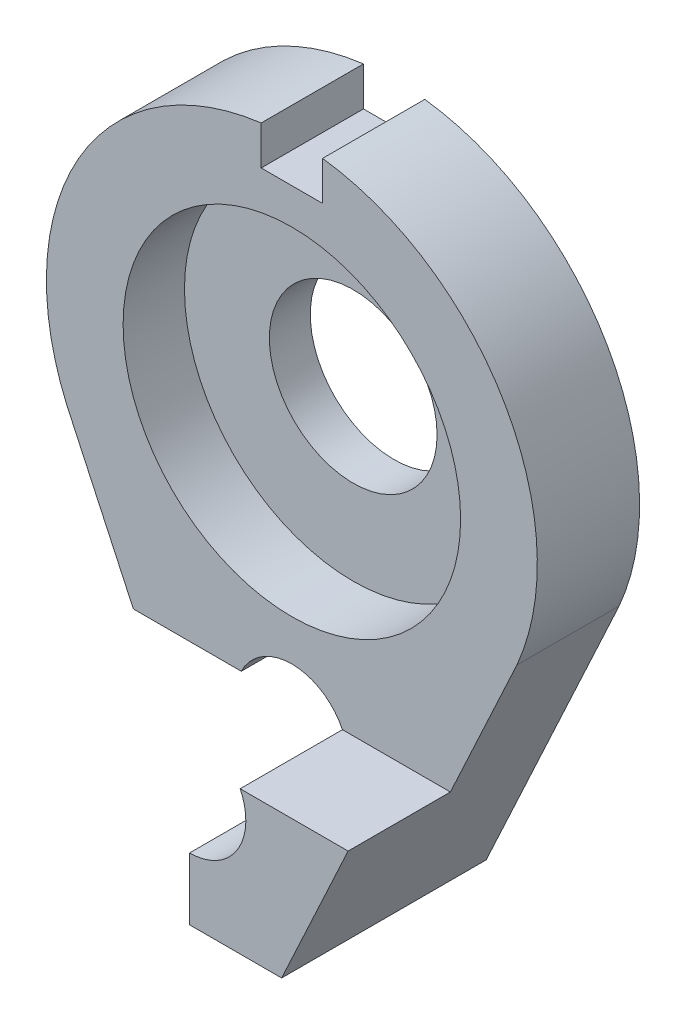
SolidWorks part; units mm, degrees
ref_plane "Plan de face" through (0, 0, 0) normal (0, 0, 1) x (1, 0, 0)
ref_plane "Plan de dessus" through (0, 0, 0) normal (0, 1, 0) x (1, 0, 0)
ref_plane "Plan de droite" through (0, 0, 0) normal (1, 0, 0) x (0, 0, -1)
sketch "Esquisse1" plane through (0, 0, 0) normal (0, 0, 1) x (1, 0, 0)
  line L0 (-11, -4.7958) -> (-4.5, -18.7958)
  line L1 (0, -55) -> (0, 55) construction
  line L2 (11, -4.7958) -> (4.5, -18.7958)
  line L3 (-4.5, -18.7958) -> (4.5, -18.7958)
  arc A0 (-11, -4.7958) -> (11, -4.7958) centre (0, 0) cw
  circle A1 centre (0, 0) radius 4.1
  dimension "D2" = 12
  dimension "D3" = 8.2
  dimension "D1" = 22
  dimension "D4" = 9
  dimension "D5" = 14
extrude "Boss.-Extru.1" add sketch "Esquisse1" along normal blind 5
sketch "Esquisse2" plane through (0, 0, 5) normal (0, 0, 1) x (1, 0, 0)
  circle A0 centre (0, 0) radius 8.25
  dimension "D1" = 16.5
extrude "Enlèv. mat.-Extru.1" cut sketch "Esquisse2" against normal blind 3
ref_plane "Plan1" through (0, 12, 0) normal (0, 1, 0) x (1, 0, 0)
sketch "Esquisse4" plane through (0, 12, 0) normal (0, 1, 0) x (1, 0, 0)
  line L0 (1.5, -5) -> (1.5, 0)
  line L1 (1.5, -5) -> (-1.5, -5)
  line L2 (1.5, 0) -> (-1.5, 0)
  line L3 (-1.5, -5) -> (-1.5, 0)
  line L4 (1.5, -5) -> (-1.5, 0) construction
  line L5 (1.5, 0) -> (-1.5, -5) construction
  line L6 (12, 0) -> (-12, 0) construction
  point P1 (0, -2.5)
  dimension "D1" = 3
  dimension "D2" = 5
extrude "Enlèv. mat.-Extru.2" cut sketch "Esquisse4" against normal blind 2 contours L0 L2 L3 L1
sketch "Esquisse6" plane through (0, 0, 5) normal (0, 0, 1) x (1, 0, 0)
  line L0 (0, -18.7958) -> (4.5, -18.7958)
  line L1 (-4.5, -18.7958) -> (4.5, -18.7958) construction
  line L2 (4.5, -18.7958) -> (7.75, -11.7958)
  line L3 (4.5, -18.7958) -> (11, -4.7958) construction
  line L4 (7.75, -11.7958) -> (0, -11.7958)
  line L5 (0, -11.7958) -> (0, -18.7958)
  dimension "D1" = 7
extrude "Boss.-Extru.2" add sketch "Esquisse6" along normal blind 5
sketch "Esquisse7" plane through (0, 0, 5) normal (0, 0, 1) x (1, 0, 0)
  line L0 (0, -18.7958) -> (0, -11.7958)
  line L1 (0, -11.7958) -> (-7.75, -11.7958)
  line L2 (-11, -4.7958) -> (-4.5, -18.7958) construction
  line L3 (-7.75, -11.7958) -> (-4.5, -18.7958)
  line L4 (-4.5, -18.7958) -> (0, -18.7958)
extrude "Enlèv. mat.-Extru.4" cut sketch "Esquisse7" against normal blind 5
sketch "Esquisse8" plane through (0, 0, 5) normal (0, 0, 1) x (1, 0, 0)
  circle A0 centre (0, -13) radius 2.75
  dimension "D1" = 5.5
  dimension "D2" = 13
extrude "Enlèv. mat.-Extru.5" cut sketch "Esquisse8" against normal through all both and the other way through all
